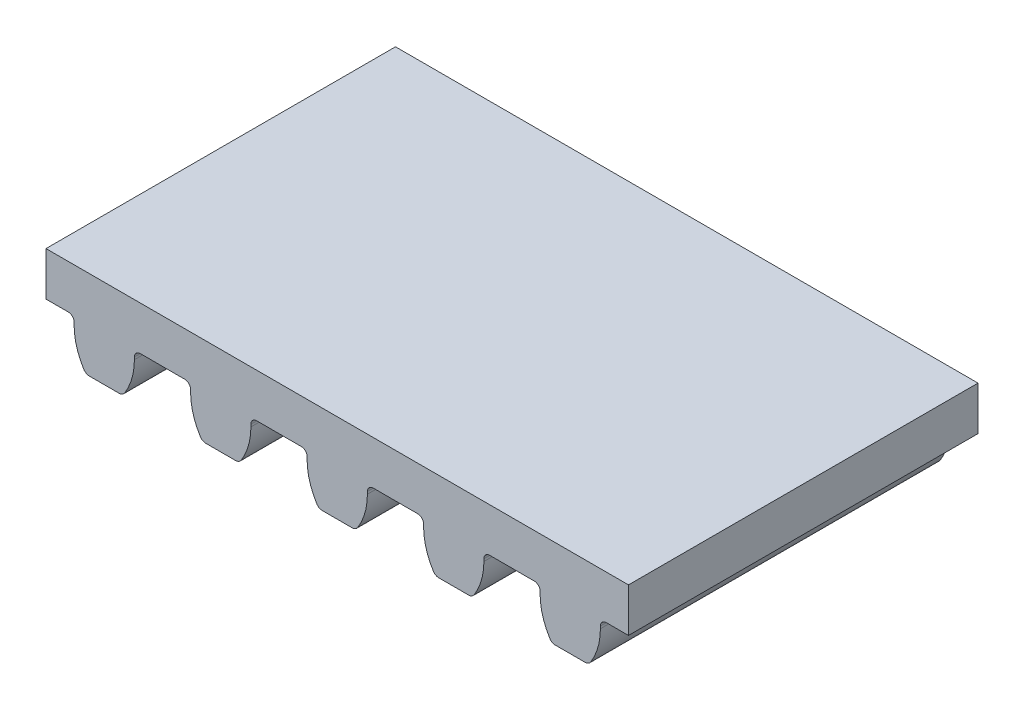
SolidWorks part; units mm, degrees
ref_plane "Front Plane" through (0, 0, 0) normal (0, 0, 1) x (1, 0, 0)
ref_plane "Top Plane" through (0, 0, 0) normal (0, 1, 0) x (1, 0, 0)
ref_plane "Right Plane" through (0, 0, 0) normal (1, 0, 0) x (0, 0, -1)
ref_plane "Plane1" through (0, 0, 15) normal (0, 0, 1) x (1, 0, 0)
sketch "Sketch1" plane through (0, 0, 15) normal (0, 0, 1) x (1, 0, 0)
  line L0 (-14.5513, 3.9796) -> (-14.5513, 4.0796)
  line L1 (-14.2973, 4.3336) -> (-12.3934, 4.3336)
  line L2 (-12.1394, 4.0796) -> (-12.1394, 3.9796)
  line L3 (-11.4837, 2.4032) -> (-10.207, 2.4032)
  line L4 (-9.5513, 3.9796) -> (-9.5513, 4.0796)
  line L5 (-9.2973, 4.3336) -> (-7.3934, 4.3336)
  line L6 (-7.1394, 4.0796) -> (-7.1394, 3.9796)
  line L7 (-6.4837, 2.4032) -> (-5.207, 2.4032)
  line L8 (-4.5513, 3.9796) -> (-4.5513, 4.0796)
  line L9 (-4.2973, 4.3336) -> (-2.3934, 4.3336)
  line L10 (-2.1394, 4.0796) -> (-2.1394, 3.9796)
  line L11 (-1.4837, 2.4032) -> (-0.207, 2.4032)
  line L12 (0.4487, 3.9796) -> (0.4487, 4.0796)
  line L13 (0.7027, 4.3336) -> (2.6066, 4.3336)
  line L14 (2.8606, 4.0796) -> (2.8606, 3.9796)
  line L15 (3.5163, 2.4032) -> (4.793, 2.4032)
  line L16 (5.4487, 3.9796) -> (5.4487, 4.0796)
  line L17 (5.7027, 4.3336) -> (6.6546, 4.3336)
  line L18 (6.6546, 4.3336) -> (6.6546, 6.2132)
  line L19 (6.6546, 6.2132) -> (-18.3453, 6.2132)
  line L20 (-18.3453, 6.2132) -> (-18.3453, 4.3336)
  line L21 (-18.3453, 4.3336) -> (-17.3934, 4.3336)
  line L22 (-17.1394, 4.0796) -> (-17.1394, 3.9796)
  line L23 (-16.4837, 2.4032) -> (-15.207, 2.4032)
  arc A0 (-14.971, 2.5331) -> (-14.5513, 3.9796) centre (-17.2541, 3.9796) ccw
  arc A1 (-14.5513, 4.0796) -> (-14.2973, 4.3336) centre (-14.2973, 4.0796) cw
  arc A2 (-12.3934, 4.3336) -> (-12.1394, 4.0796) centre (-12.3934, 4.0796) cw
  arc A3 (-12.1394, 3.9796) -> (-11.7197, 2.5331) centre (-9.4366, 3.9796) ccw
  arc A4 (-11.7197, 2.5331) -> (-11.4837, 2.4032) centre (-11.4837, 2.6826) ccw
  arc A5 (-10.207, 2.4032) -> (-9.971, 2.5331) centre (-10.207, 2.6826) ccw
  arc A6 (-9.971, 2.5331) -> (-9.5513, 3.9796) centre (-12.2541, 3.9796) ccw
  arc A7 (-9.5513, 4.0796) -> (-9.2973, 4.3336) centre (-9.2973, 4.0796) cw
  arc A8 (-7.3934, 4.3336) -> (-7.1394, 4.0796) centre (-7.3934, 4.0796) cw
  arc A9 (-7.1394, 3.9796) -> (-6.7197, 2.5331) centre (-4.4366, 3.9796) ccw
  arc A10 (-6.7197, 2.5331) -> (-6.4837, 2.4032) centre (-6.4837, 2.6826) ccw
  arc A11 (-5.207, 2.4032) -> (-4.971, 2.5331) centre (-5.207, 2.6826) ccw
  arc A12 (-4.971, 2.5331) -> (-4.5513, 3.9796) centre (-7.2541, 3.9796) ccw
  arc A13 (-4.5513, 4.0796) -> (-4.2973, 4.3336) centre (-4.2973, 4.0796) cw
  arc A14 (-2.3934, 4.3336) -> (-2.1394, 4.0796) centre (-2.3934, 4.0796) cw
  arc A15 (-2.1394, 3.9796) -> (-1.7197, 2.5331) centre (0.5634, 3.9796) ccw
  arc A16 (-1.7197, 2.5331) -> (-1.4837, 2.4032) centre (-1.4837, 2.6826) ccw
  arc A17 (-0.207, 2.4032) -> (0.029, 2.5331) centre (-0.207, 2.6826) ccw
  arc A18 (0.029, 2.5331) -> (0.4487, 3.9796) centre (-2.2541, 3.9796) ccw
  arc A19 (0.4487, 4.0796) -> (0.7027, 4.3336) centre (0.7027, 4.0796) cw
  arc A20 (2.6066, 4.3336) -> (2.8606, 4.0796) centre (2.6066, 4.0796) cw
  arc A21 (2.8606, 3.9796) -> (3.2803, 2.5331) centre (5.5634, 3.9796) ccw
  arc A22 (3.2803, 2.5331) -> (3.5163, 2.4032) centre (3.5163, 2.6826) ccw
  arc A23 (4.793, 2.4032) -> (5.029, 2.5331) centre (4.793, 2.6826) ccw
  arc A24 (5.029, 2.5331) -> (5.4487, 3.9796) centre (2.7459, 3.9796) ccw
  arc A25 (5.4487, 4.0796) -> (5.7027, 4.3336) centre (5.7027, 4.0796) cw
  arc A26 (-17.3934, 4.3336) -> (-17.1394, 4.0796) centre (-17.3934, 4.0796) cw
  arc A27 (-17.1394, 3.9796) -> (-16.7197, 2.5331) centre (-14.4366, 3.9796) ccw
  arc A28 (-16.7197, 2.5331) -> (-16.4837, 2.4032) centre (-16.4837, 2.6826) ccw
  arc A29 (-15.207, 2.4032) -> (-14.971, 2.5331) centre (-15.207, 2.6826) ccw
extrude "Extrude1" add sketch "Sketch1" against normal blind 15
